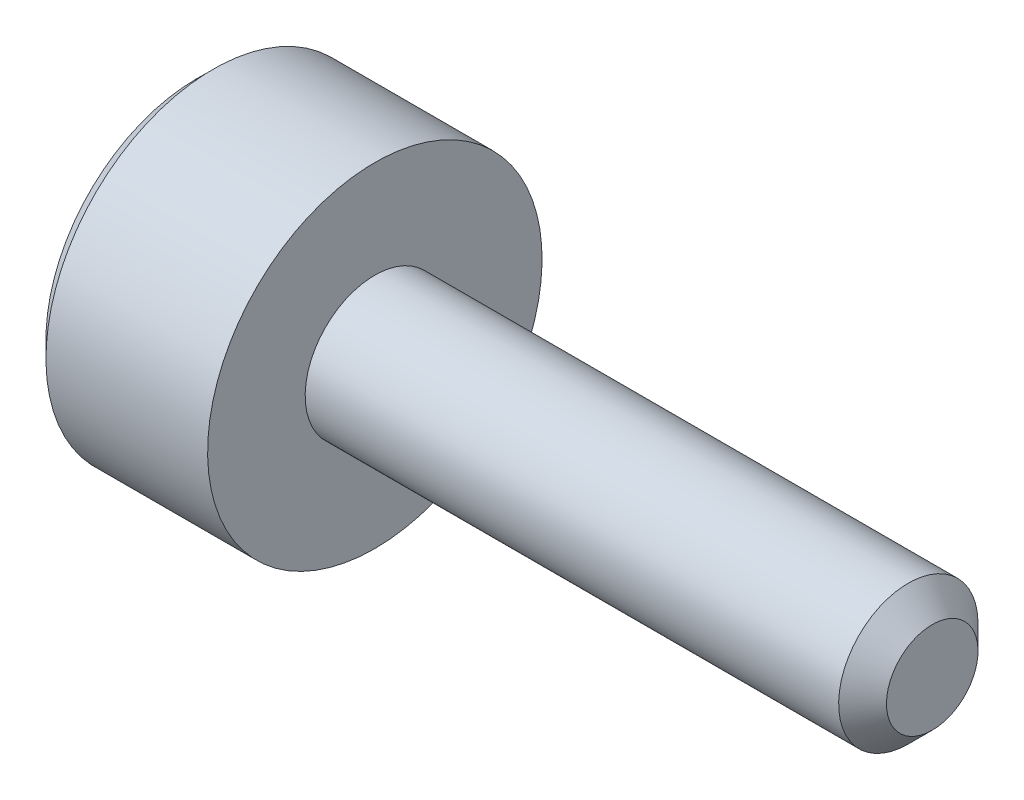
SolidWorks part; units mm, degrees
material "AISI 304"
ref_plane "正面" through (0, 0, 0) normal (0, 0, 1) x (1, 0, 0)
ref_plane "平面" through (0, 0, 0) normal (0, 1, 0) x (1, 0, 0)
ref_plane "右側面" through (0, 0, 0) normal (1, 0, 0) x (0, 0, -1)
ref_plane "Plane1" through (0, 0, 0) normal (0, 0, 1) x (1, 0, 0)
sketch "Sketch1" plane through (0, 0, 0) normal (0, 0, 1) x (1, 0, 0)
  line L0 (-1.6, 0) -> (-1.6, 1.35)
  line L1 (-1.6, 1.35) -> (-1.45, 1.5)
  line L2 (-1.45, 1.5) -> (0, 1.5)
  line L3 (0, 1.5) -> (0, 0.625)
  line L4 (0, 0.625) -> (4.7855, 0.625)
  line L5 (4.7855, 0.625) -> (5, 0.4105)
  line L6 (5, 0.4105) -> (5, 0)
  line L7 (5, 0) -> (-1.6, 0)
  line L8 (5, 0) -> (-1.6, 0) construction
  dimension "D1" = 0.625
  dimension "D2" = 1.6
  dimension "D3" = 6.6
revolve "Revolve1" add sketch "Sketch1" angle 360 about L8
cosmetic thread "Cosmetic Thread1" parameters "D1"=5.6276, "D2"=1.171
ref_plane "Plane2" through (-1.6, 0, 0) normal (1, 0, 0) x (0, 0, -1)
sketch "Sketch2" plane through (-1.6, 0, 0) normal (1, 0, 0) x (0, 0, -1)
  line L0 (-0.75, -0.433) -> (0, -0.866)
  line L1 (0, -0.866) -> (0.75, -0.433)
  line L2 (0.75, -0.433) -> (0.75, 0.433)
  line L3 (0.75, 0.433) -> (0, 0.866)
  line L4 (0, 0.866) -> (-0.75, 0.433)
  line L5 (-0.75, 0.433) -> (-0.75, -0.433)
extrude "Cut-Extrude1" cut sketch "Sketch2" along normal blind 0.64
